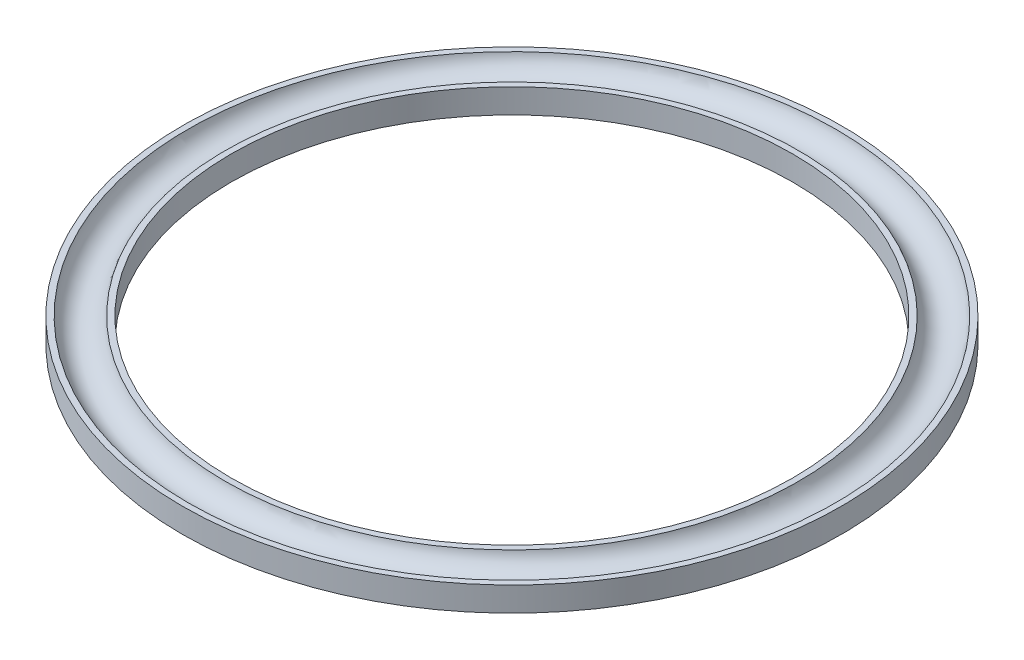
SolidWorks part; units mm, degrees
ref_plane "Front Plane" through (0, 0, 0) normal (0, 0, 1) x (1, 0, 0)
ref_plane "Top Plane" through (0, 0, 0) normal (0, 1, 0) x (1, 0, 0)
ref_plane "Right Plane" through (0, 0, 0) normal (1, 0, 0) x (0, 0, -1)
sketch "Sketch2" plane through (0, 0, 0) normal (0, 0, 1) x (1, 0, 0)
  line L0 (0, 30.7124) -> (0, -49.8925) construction
  line L7 (-46, -4.2) -> (-46, -6.7)
  line L8 (-54, -4.2) -> (-54, -8.2)
  line L9 (-54, -8.2) -> (-46, -8.2)
  line L10 (-46, -4.2) -> (-46.9586, -4.2)
  line L14 (-53.0414, -4.2) -> (-54, -4.2)
  line L15 (-46, -8.2) -> (-46, -6.7)
  arc A1 (-53.0414, -4.2) -> (-46.9586, -4.2) centre (-50, -3.6) ccw
  dimension "D1" = 1.5
  dimension "D6" = 2.5
revolve "Revolve2" add sketch "Sketch2" angle 360 about L0
sketch "Sketch4" plane through (0, -8.2, 0) normal (0, -1, 0) x (1, 0, 0)
  line L0 (-49.6063, 0) -> (-51.2841, 0)
  line L1 (-47.0681, 0) -> (-48.8893, 0)
  line L2 (-48.8893, 0) -> (-48.8893, -0.7089)
  line L3 (-48.8893, -0.7089) -> (-48.1293, -0.7089)
  line L4 (-48.1293, -0.7089) -> (-48.8893, -3.0176)
  line L5 (-48.8893, -3.0176) -> (-47.8281, -3.0176)
  line L6 (-47.8281, -3.0176) -> (-47.0681, -0.7089)
  line L7 (-47.0681, 0) -> (-47.0681, -0.7089)
  line L8 (-51.2841, 0) -> (-51.2841, -1.5693)
  line L9 (-51.2841, -1.5693) -> (-50.0867, -1.5693)
  line L10 (-50.0867, -1.5693) -> (-50.0867, -3.0176)
  line L11 (-50.0867, -3.0176) -> (-49.6063, -3.0176)
  line L12 (-49.6063, -3.0176) -> (-49.6063, -1.5693)
  line L13 (-49.6063, -1.5693) -> (-49.6063, 0)
  line L14 (-50.7678, -0.3934) -> (-50.0867, -0.3934)
  line L15 (-50.0867, -0.3934) -> (-50.0867, -0.924)
  line L16 (-50.0867, -0.924) -> (-50.7678, -0.924)
  line L17 (-50.7678, -0.924) -> (-50.7678, -0.3934)
extrude "Cut-Extrude1" cut sketch "Sketch4" against normal blind 0.3
